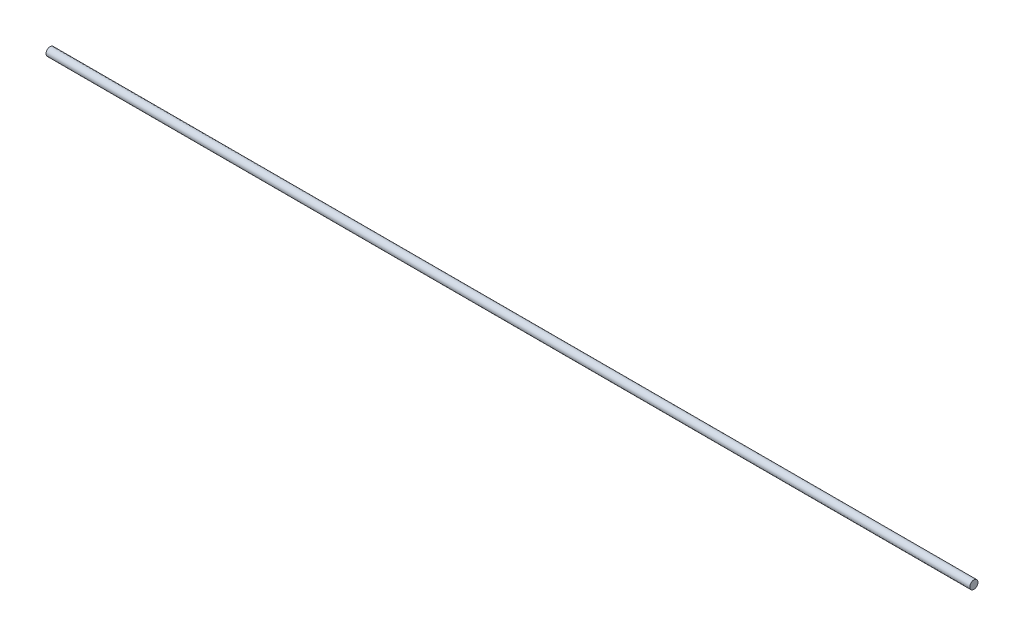
SolidWorks part; units mm, degrees
ref_plane "Front Plane" through (0, 0, 0) normal (0, 0, 1) x (1, 0, 0)
ref_plane "Top Plane" through (0, 0, 0) normal (0, 1, 0) x (1, 0, 0)
ref_plane "Right Plane" through (0, 0, 0) normal (1, 0, 0) x (0, 0, -1)
sketch "Sketch1" plane through (0, 0, 0) normal (1, 0, 0) x (0, 0, -1)
  circle A0 centre (0, 0) radius 3.175
  dimension "D1" = 6.35
extrude "Boss-Extrude1" add sketch "Sketch1" along normal blind 711.2 contours A0
